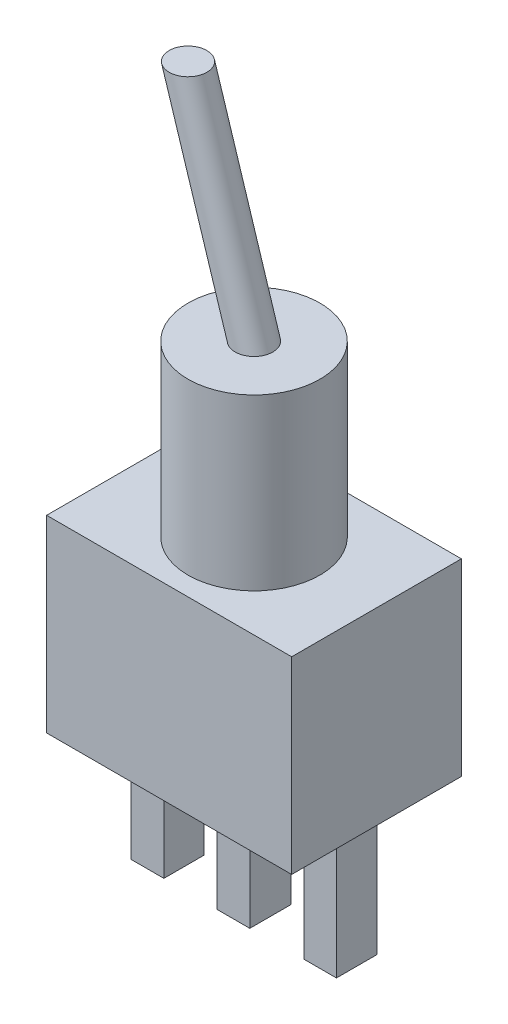
SolidWorks part; units mm, degrees
ref_plane "Front" through (0, 0, 0) normal (0, 0, 1) x (1, 0, 0)
ref_plane "Top" through (0, 0, 0) normal (0, 1, 0) x (1, 0, 0)
ref_plane "Right" through (0, 0, 0) normal (1, 0, 0) x (0, 0, -1)
sketch "草图1" plane through (0, 0, 0) normal (0, 1, 0) x (1, 0, 0)
  line L1 (-6.5, 4.5) -> (6.5, 4.5)
  line L2 (-6.5, 4.5) -> (-6.5, -4.5)
  line L3 (-6.5, -4.5) -> (6.5, -4.5)
  line L4 (6.5, 4.5) -> (6.5, -4.5)
  line L5 (-6.5, 4.5) -> (6.5, -4.5) construction
  line L6 (-6.5, -4.5) -> (6.5, 4.5) construction
  point P0 (0, 0)
  dimension "D1" = 13
  dimension "D2" = 9
extrude "凸台-拉伸1" add sketch "草图1" along normal blind 10
sketch "草图2" plane through (0, 10, 0) normal (0, 1, 0) x (1, 0, 0)
  circle A0 centre (0, 0) radius 3.5
extrude "凸台-拉伸2" add sketch "草图2" along normal blind 9
sketch "草图3" plane through (0, 0, 0) normal (0, 0, 1) x (1, 0, 0)
  line L0 (0, 19) -> (-3.5, 30.1002)
  line L1 (3.5, 19) -> (-3.5, 19) construction
sketch "草图4" plane through (0, 19, 0) normal (0, 1, 0) x (1, 0, 0)
  circle A0 centre (0, 0) radius 1
sweep "扫描1" add profiles "草图4" path "草图3"
sketch "草图5" plane through (0, 0, 0) normal (0, -1, 0) x (-1, 0, 0)
  line L0 (0, -2.9265) -> (0, 3.354) construction
  line L1 (-3.7101, -1.0698) -> (-5.4432, -1.0698)
  line L2 (-3.7101, -1.0698) -> (-3.7101, 1.0698)
  line L3 (-3.7101, 1.0698) -> (-5.4432, 1.0698)
  line L4 (-5.4432, -1.0698) -> (-5.4432, 1.0698)
  line L5 (-3.7101, -1.0698) -> (-5.4432, 1.0698) construction
  line L6 (-3.7101, 1.0698) -> (-5.4432, -1.0698) construction
  line L7 (3.7101, 1.0698) -> (5.4432, 1.0698)
  line L8 (5.4432, -1.0698) -> (5.4432, 1.0698)
  line L9 (3.7101, -1.0698) -> (5.4432, -1.0698)
  line L10 (3.7101, -1.0698) -> (3.7101, 1.0698)
  line L12 (0.8647, -1.0874) -> (-0.8647, -1.0874)
  line L13 (0.8647, -1.0874) -> (0.8647, 1.0874)
  line L14 (0.8647, 1.0874) -> (-0.8647, 1.0874)
  line L15 (-0.8647, -1.0874) -> (-0.8647, 1.0874)
  line L16 (0.8647, -1.0874) -> (-0.8647, 1.0874) construction
  line L17 (0.8647, 1.0874) -> (-0.8647, -1.0874) construction
  point P0 (-4.5766, 0)
  point P12 (0, 0)
  point P19 (3.7101, 0)
extrude "凸台-拉伸3" add sketch "草图5" along normal blind 7
